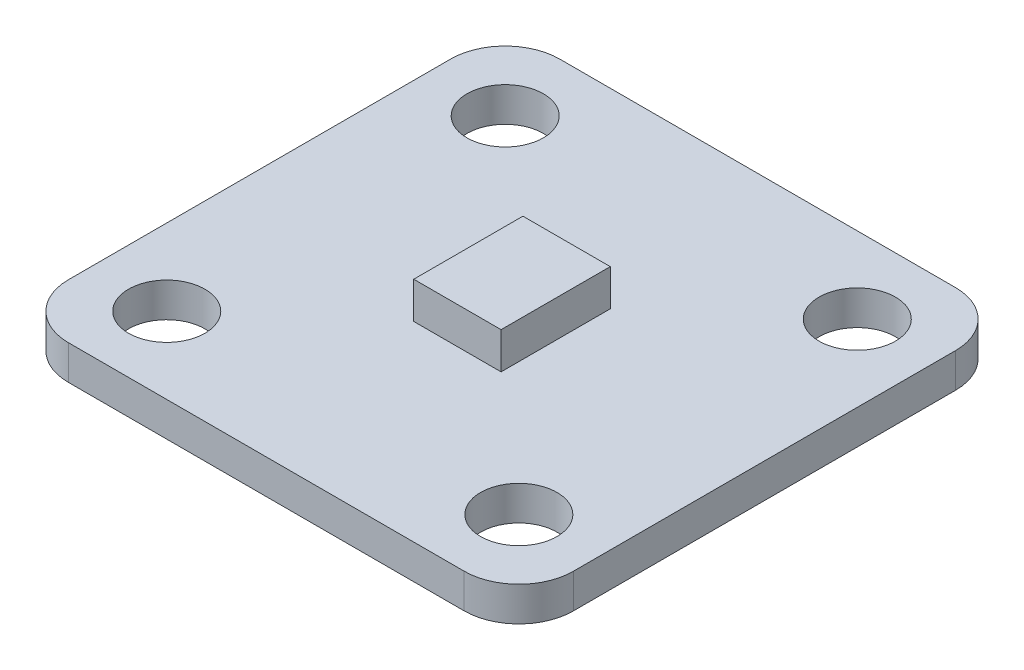
SolidWorks part; units mm, degrees
ref_plane "Front Plane" through (0, 0, 0) normal (0, 0, 1) x (1, 0, 0)
ref_plane "Top Plane" through (0, 0, 0) normal (0, 1, 0) x (1, 0, 0)
ref_plane "Right Plane" through (0, 0, 0) normal (1, 0, 0) x (0, 0, -1)
sketch "Sketch1" plane through (0, 0, 0) normal (0, 1, 0) x (1, 0, 0)
  line L1 (-11.7475, -11.43) -> (11.7475, -11.43)
  line L2 (-11.7475, -11.43) -> (-11.7475, 11.43)
  line L3 (-11.7475, 11.43) -> (11.7475, 11.43)
  line L4 (11.7475, -11.43) -> (11.7475, 11.43)
  line L5 (-11.7475, -11.43) -> (11.7475, 11.43) construction
  line L6 (-11.7475, 11.43) -> (11.7475, -11.43) construction
  point P0 (0, 0)
  dimension "D1" = 23.495
  dimension "D2" = 22.86
extrude "Boss-Extrude1" add sketch "Sketch1" along normal blind 1.6002
sketch "Sketch2" plane through (0, 1.6002, 0) normal (0, 1, 0) x (1, 0, 0)
  line L1 (-2.032, -2.54) -> (2.032, -2.54)
  line L2 (-2.032, -2.54) -> (-2.032, 2.54)
  line L3 (-2.032, 2.54) -> (2.032, 2.54)
  line L4 (2.032, -2.54) -> (2.032, 2.54)
  line L5 (-2.032, -2.54) -> (2.032, 2.54) construction
  line L6 (-2.032, 2.54) -> (2.032, -2.54) construction
  point P0 (0, 0)
  dimension "D1" = 5.08
  dimension "D2" = 4.064
extrude "Boss-Extrude2" add sketch "Sketch2" along normal blind 1.7018
fillet "Fillet1" radius 2.54 4 edges at (-11.7475, 0.8001, -11.43) (11.7475, 0.8001, -11.43) (11.7475, 0.8001, 11.43) (-11.7475, 0.8001, 11.43)
sketch "Sketch4" plane through (0, 1.6002, 0) normal (0, 1, 0) x (1, 0, 0)
  line L0 (-11.7475, 8.89) -> (-11.7475, -8.89) construction
  line L1 (8.1915, -7.874) -> (-8.1915, -7.874) construction
  line L2 (8.1915, -7.874) -> (8.1915, 7.874) construction
  line L3 (8.1915, 7.874) -> (-8.1915, 7.874) construction
  line L4 (-8.1915, -7.874) -> (-8.1915, 7.874) construction
  line L5 (8.1915, -7.874) -> (-8.1915, 7.874) construction
  line L6 (8.1915, 7.874) -> (-8.1915, -7.874) construction
  line L7 (-9.2075, -11.43) -> (9.2075, -11.43) construction
  line L8 (11.7475, -8.89) -> (11.7475, 8.89) construction
  line L9 (9.2075, 11.43) -> (-9.2075, 11.43) construction
  circle A0 centre (-8.1915, -7.874) radius 1.778
  circle A1 centre (-8.1915, 7.874) radius 1.778
  circle A2 centre (8.1915, 7.874) radius 1.778
  circle A3 centre (8.1915, -7.874) radius 1.778
  point P0 (0, 0)
  point P10 (-8.1915, -9.652)
  point P11 (-9.9695, -7.874)
  point P16 (9.9695, -7.874)
  point P17 (8.1915, 9.652)
  dimension "D1" = 3.556
  dimension "D2" = 1.778
  dimension "D3" = 1.778
  dimension "D4" = 1.778
  dimension "D5" = 1.778
extrude "Cut-Extrude1" cut sketch "Sketch4" against normal through all
